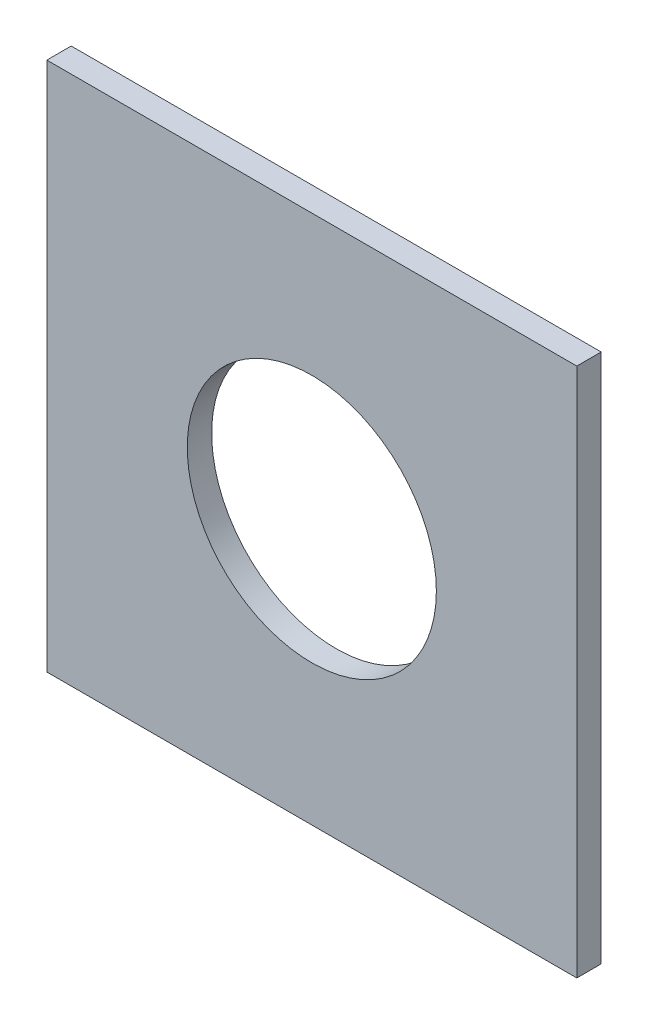
SolidWorks part; units mm, degrees
ref_plane "Plan de face" through (0, 0, 0) normal (0, 0, 1) x (1, 0, 0)
ref_plane "Plan de dessus" through (0, 0, 0) normal (0, 1, 0) x (1, 0, 0)
ref_plane "Plan de droite" through (0, 0, 0) normal (1, 0, 0) x (0, 0, -1)
sketch "Esquisse1" plane through (0, 0, 0) normal (0, 0, 1) x (1, 0, 0)
  line L1 (-44.1717, 36.1501) -> (55.8283, 36.1501)
  line L2 (-44.1717, 36.1501) -> (-44.1717, -13.8499)
  line L3 (-44.1717, -13.8499) -> (55.8283, -13.8499)
  line L4 (55.8283, 36.1501) -> (55.8283, -13.8499)
  line L6 (-44.1717, -13.8499) -> (55.8283, -13.8499)
  line L7 (-44.1717, -13.8499) -> (-44.1717, -63.8499)
  line L8 (-44.1717, -63.8499) -> (55.8283, -63.8499)
  line L9 (55.8283, -13.8499) -> (55.8283, -63.8499)
  arc A0 (29.3283, -13.8499) -> (-17.6717, -13.8499) centre (5.8283, -13.8499) ccw
  circle A1 centre (5.8283, -13.8499) radius 23.5
  dimension "D1" = 23.5
  dimension "D2" = 100
  dimension "D3" = 50
  dimension "D4" = 50
extrude "Boss.-Extru.1" add sketch "Esquisse1" along normal blind 4.6 contours A0 L3 L4 L1 L2 | A1 L3 L7 L8 L9
